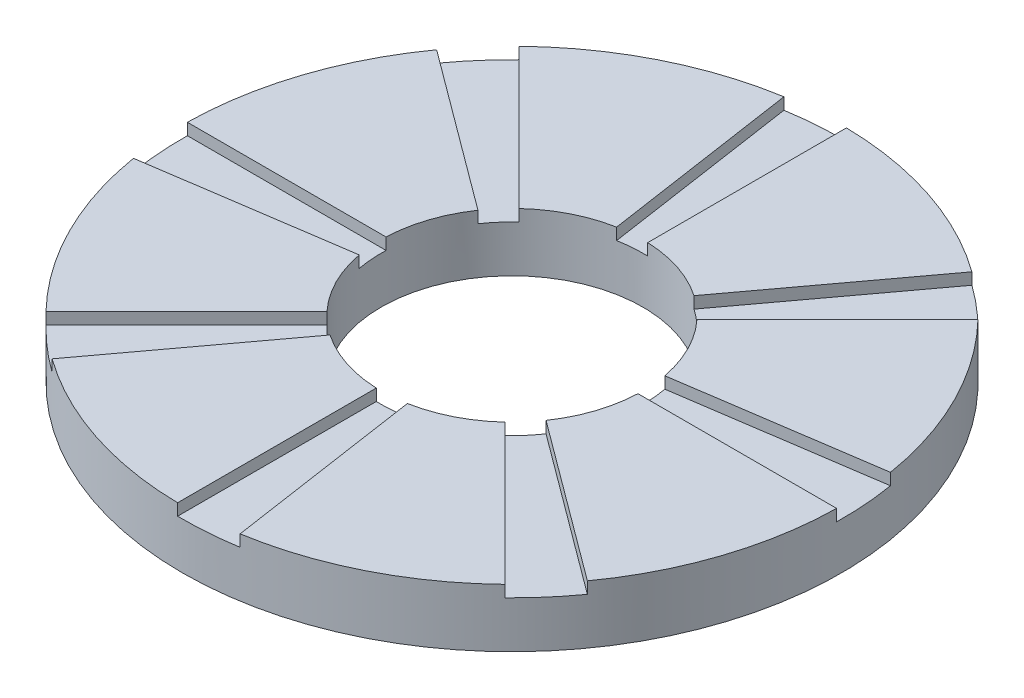
SolidWorks part; units mm, degrees
ref_plane "Front Plane" through (0, 0, 0) normal (0, 0, 1) x (1, 0, 0)
ref_plane "Top Plane" through (0, 0, 0) normal (0, 1, 0) x (1, 0, 0)
ref_plane "Right Plane" through (0, 0, 0) normal (1, 0, 0) x (0, 0, -1)
sketch "Sketch1" plane through (0, 0, 0) normal (0, 1, 0) x (1, 0, 0)
  circle A0 centre (0, 0) radius 56.4862
  circle A1 centre (0, 0) radius 22.4405
extrude "Boss-Extrude1" add sketch "Sketch1" along normal blind 10
sketch "Sketch2" plane through (0, 10, 0) normal (0, 1, 0) x (1, 0, 0)
  line L0 (-1.4201, 3.8553) -> (-9.1351, 55.7426)
  line L1 (0.8376, 4.0222) -> (0.8376, 56.48)
  line L2 (0, 0) -> (-4.1651, 56.3324) construction
  line L3 (-4.1651, 56.3324) -> (0.8376, 56.48) construction
  line L4 (-4.1651, 56.3324) -> (-9.1351, 55.7426) construction
  circle A1 centre (0, 0) radius 4.1085
  circle A2 centre (0, 0) radius 56.4862 construction
  circle A4 centre (0, 0) radius 56.4862
  arc A5 (0.8376, 56.48) -> (-9.1351, 55.7426) centre (0, 0) ccw
  circle M7 centre (0, 0) radius 56.4862
  circle M8 centre (0, 0) radius 22.4405
  dimension "D1" = 10
  dimension "D2" = 0
extrude "Cut-Extrude1" cut sketch "Sketch2" against normal blind 2 contours A1 L1 L0 M8 | L1 L0 M8 M7
pattern_circular "CirPattern1" count 8 over 360 about axis through (0, 0, 0) along (0, 1, 0) of "Cut-Extrude1"
